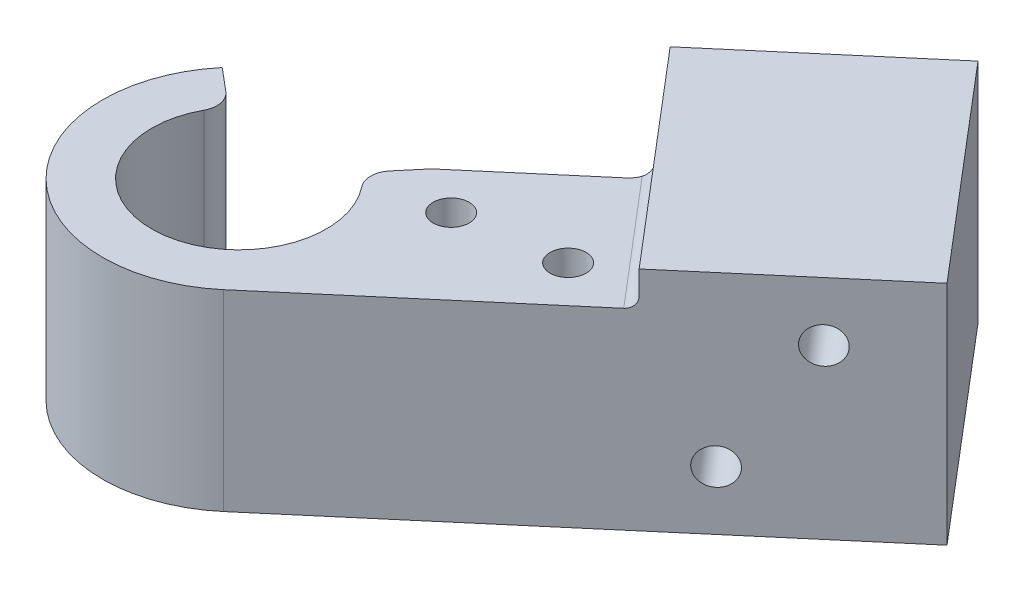
SolidWorks part; units mm, degrees
material "6061-T6 (SS)"
ref_plane "Front Plane" through (0, 0, 0) normal (0, 0, 1) x (1, 0, 0)
ref_plane "Top Plane" through (0, 0, 0) normal (0, 1, 0) x (1, 0, 0)
ref_plane "Right Plane" through (0, 0, 0) normal (1, 0, 0) x (0, 0, -1)
sketch "Sketch1" plane through (0, 0, 0) normal (0, 1, 0) x (1, 0, 0)
  circle A0 centre (0, 0) radius 12.5
  dimension "D2" = 25
extrude "Boss-Extrude1" add sketch "Sketch1" along normal blind 17.6
sketch "Sketch2" plane through (0, 17.6, 0) normal (0, 1, 0) x (1, 0, 0)
  circle A0 centre (0, 0) radius 6.875
  dimension "D1" = 13.75
extrude "Cut-Extrude1" cut sketch "Sketch2" against normal blind 50.8
sketch "Sketch3" plane through (0, 17.6, 0) normal (0, 1, 0) x (1, 0, 0)
  circle A0 centre (0, 0) radius 8
  dimension "D1" = 16
extrude "Cut-Extrude3" cut sketch "Sketch3" against normal offset from surface (15.6 mm away) 2 up to face at (0, 0, 6.875)
sketch "Sketch4" plane through (0, 17.6, 0) normal (0, 1, 0) x (1, 0, 0)
  line L0 (0, 0) -> (14.4876, 17.2657)
  line L1 (0, 0) -> (-19.972, 16.7585)
  line L2 (0, 0) -> (0, 22.9529) construction
  line L3 (0, 0) -> (-17.2058, 0) construction
  circle A0 centre (0, 0) radius 8 construction
  circle A1 centre (0, 0) radius 12.5 construction
  circle A2 centre (0, 0) radius 8
  circle A3 centre (0, 0) radius 12.5
  circle M3 centre (0, 0) radius 8
  circle M4 centre (0, 0) radius 12.5
  dimension "D1" = 90
  dimension "D2" = 40
extrude "Cut-Extrude4" cut sketch "Sketch4" against normal through all contours L1 L0 M3 M4
sketch "Sketch5" plane through (0, 17.6, 0) normal (0, 1, 0) x (1, 0, 0)
  line L0 (19.2118, 19.0856) -> (8.0348, 9.5756)
  line L1 (8.1004, -9.5202) -> (28.664, 7.9766)
  line L2 (28.664, 7.9766) -> (19.2118, 19.0856)
  arc A0 (-9.5756, 8.0348) -> (8.0348, 9.5756) centre (0, 0) ccw construction
  arc A1 (-9.5756, 8.0348) -> (8.0348, 9.5756) centre (0, 0) ccw
  dimension "D1" = 27
extrude "Boss-Extrude2" add sketch "Sketch5" against normal through all
fillet "Fillet1" radius 2 2 edges at (-6.1284, 9.8, -5.1423) (5.1423, 9.8, -6.1284)
sketch "Sketch6" plane through (20.5636, 0, -17.4968) normal (0.7616, 0, -0.648) x (-0.648, 0, -0.7616)
  line L0 (-12.5, 17.6) -> (2.0861, 17.6) construction
  line L1 (-12.5, 0) -> (12.5, 0)
  line L2 (-12.5, 0) -> (-12.5, 20.775)
  line L3 (-12.5, 20.775) -> (12.5, 20.775)
  line L4 (12.5, 0) -> (12.5, 20.775)
  point P4 (0, 0)
  dimension "D1" = 3.175
  dimension "D2" = 25
extrude "Boss-Extrude3" add sketch "Sketch6" along normal blind 20
hole_wizard "M4x0.7 Tapped Hole2" positions "Sketch7" profile "Sketch9" tap size "M4x0.7" standard "ANSI Metric"
sketch "Sketch7" plane through (-8.1004, 0, -9.5202) normal (-0.648, 0, -0.7616) x (-0.7616, 0, 0.648)
  line L0 (-39, 15.3875) -> (-32, 5.3875) construction
  line L2 (-27, 0) -> (-27, 20.775) construction
  line L3 (-47, 10.3875) -> (-28.7744, 10.3875) construction
  line L4 (-47, 0) -> (-47, 20.775) construction
  point P0 (-39, 15.3875)
  point P2 (-32, 5.3875)
  point P18 (-35.5, 10.3875)
  dimension "D1" = 7
  dimension "D2" = 10
  dimension "D3" = 5
sketch "Sketch9" plane through (21.6026, 15.3875, -34.7933) normal (0, 1, 0) x (-0.7616, 0, 0.648)
  line L0 (0, 0) -> (0, 7.9914)
  line L1 (0, 7.9914) -> (1.65, 7)
  line L2 (1.65, 7) -> (1.65, 0)
  line L5 (1.65, 0) -> (0, 0)
  line L10 (0, 7.9914) -> (-1.65, 7) construction
  line L11 (0, -6.35) -> (0, 107.95) construction
  dimension "Tap Drill Dia." = 3.3
  dimension "Tap Drill Depth" = 7
  dimension "Drill Angle" = 118
ref_plane "Plane1" through (0, 0, 0) normal (-0.648, 0, -0.7616) x (-0.7616, 0, 0.648)
mirror "Mirror1" about plane through (0, 0, 0) normal (-0.648, 0, -0.7616) of "M4x0.7 Tapped Hole2"
hole_wizard "M4x0.7 Tapped Hole1" positions "Sketch10" profile "Sketch11" tap size "M4x0.7" standard "ANSI Metric"
sketch "Sketch10" plane through (0, 17.6, 0) normal (0, 1, 0) x (1, 0, 0)
  line L2 (23.9379, 13.5311) -> (11.6934, 3.1127)
  line L3 (28.664, 7.9766) -> (19.2118, 19.0856) construction
  line L5 (21.7499, 8.3869) -> (15.657, 3.2027)
  line L6 (15.657, 3.2027) -> (12.4168, 7.0108)
  line L7 (12.4168, 7.0108) -> (21.7499, 8.3869)
  point P0 (21.7499, 8.3869)
  point P2 (12.4168, 7.0108)
  point P23 (17.0833, 7.6988)
  dimension "D1" = 5
  dimension "D2" = 8
  dimension "D3" = 5
sketch "Sketch11" plane through (21.7499, 17.6, -8.3869) normal (1, 0, 0) x (0, 0, 1)
  line L0 (0, 0) -> (0, 7.9914)
  line L1 (0, 7.9914) -> (1.65, 7)
  line L2 (1.65, 7) -> (1.65, 0)
  line L5 (1.65, 0) -> (0, 0)
  line L10 (0, 7.9914) -> (-1.65, 7) construction
  line L11 (0, -6.35) -> (0, 107.95) construction
  dimension "Tap Drill Dia." = 3.3
  dimension "Tap Drill Depth" = 7
  dimension "Drill Angle" = 118
cosmetic thread "Hole Thread1" parameters "D1"=7, "D2"=4
cosmetic thread "Hole Thread2" parameters "D1"=7, "D2"=4
fillet "Fillet4" radius 1 1 edges at (23.9379, 17.6, -13.5311)
fillet "Fillet6" radius 1 2 edges at (-6.1284, 1, -5.1423) (5.1423, 1, -6.1284)
fillet "Fillet7" radius 2 1 edges at (19.2118, 9.3, -19.0856)
equation "\"1.1c\"=0.0104601"
